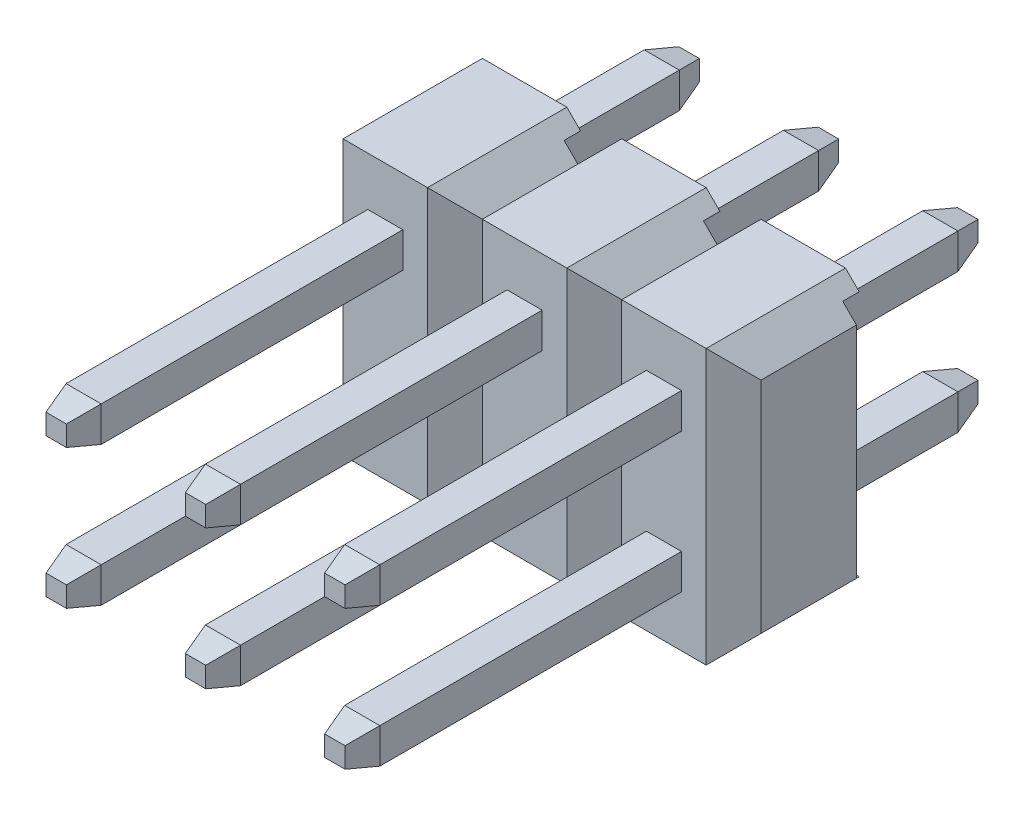
SolidWorks part; units mm, degrees
ref_plane "Front Plane" through (0, 0, 0) normal (0, 0, 1) x (1, 0, 0)
ref_plane "Top Plane" through (0, 0, 0) normal (0, 1, 0) x (1, 0, 0)
ref_plane "Right Plane" through (0, 0, 0) normal (1, 0, 0) x (0, 0, -1)
sketch "Sketch2" plane through (0, 0, 0) normal (0, 0, 1) x (1, 0, 0)
  line L1 (0, 0) -> (2.54, 0)
  line L2 (0, 0) -> (0, 5)
  line L3 (0, 5) -> (2.54, 5)
  line L4 (2.54, 0) -> (2.54, 5)
  dimension "length" = 2.54
  dimension "width" = 5
extrude "Boss-Extrude1" add sketch "Sketch2" along normal blind 2.54
sketch "Sketch3" plane through (0, 0, 0) normal (-1, 0, 0) x (0, 0, 1)
  line L0 (0, 2.5) -> (2.54, 2.5) construction
  line L1 (0, 5) -> (0, 0) construction
  line L2 (2.54, 5) -> (2.54, 0) construction
  line L3 (2.54, 5) -> (0, 5) construction
  line L4 (0, 4.75) -> (0.3, 4.75)
  line L5 (0, 4.75) -> (0, 0.25)
  line L6 (0, 0.25) -> (0.3, 0.25)
  line L7 (0.3, 4.75) -> (0.3, 0.25)
  point P10 (0, 2.5)
  dimension "D1" = 0.25
  dimension "D2" = 0.3
extrude "Cut-Extrude1" cut sketch "Sketch3" against normal through all
chamfer "Chamfer1" distance 0.5 angle 45 4 edges at (2.54, 5, 1.27) (2.54, 0, 1.27) (0, 5, 1.27) (0, 0, 1.27)
chamfer "Chamfer2" distance 0.5 angle 45 2 edges at (2.54, 2.5, 2.54) (0, 2.5, 2.54)
sketch "Sketch4" plane through (0, 0, 2.54) normal (0, 0, 1) x (1, 0, 0)
  line L0 (0.5, 1.25) -> (2.04, 1.25) construction
  line L1 (0.5, 5) -> (0.5, 0) construction
  line L2 (2.04, 0) -> (2.04, 5) construction
  line L3 (0.5, 0) -> (2.04, 0) construction
  line L4 (1.27, 5) -> (1.27, 0) construction
  line L5 (2.04, 5) -> (0.5, 5) construction
  line L7 (0.95, 1.57) -> (1.59, 1.57)
  line L8 (0.95, 1.57) -> (0.95, 0.93)
  line L9 (0.95, 0.93) -> (1.59, 0.93)
  line L10 (1.59, 1.57) -> (1.59, 0.93)
  point P16 (1.59, 1.25)
  point P17 (1.27, 1.57)
  dimension "D1" = 1.25
  dimension "D2" = 0.64
extrude "Boss-Extrude2" add sketch "Sketch4" along normal blind 6 separate body
sketch "Sketch6" plane through (0, 0, 0.3) normal (0, 0, -1) x (-1, 0, 0)
  line L1 (-1.59, 1.57) -> (-0.95, 1.57)
  line L2 (-1.59, 1.57) -> (-1.59, 0.93)
  line L3 (-1.59, 0.93) -> (-0.95, 0.93)
  line L4 (-0.95, 1.57) -> (-0.95, 0.93)
extrude "Boss-Extrude3" add sketch "Sketch6" along normal blind 3.3 separate body
chamfer "Chamfer3" distance 0.5 angle 15 4 edges at (1.27, 1.57, 8.54) (1.59, 1.25, 8.54) (1.27, 0.93, 8.54) (0.95, 1.25, 8.54)
chamfer "Chamfer4" distance 0.5 angle 15 4 edges at (1.27, 1.57, -3) (0.95, 1.25, -3) (1.27, 0.93, -3) (1.59, 1.25, -3)
pattern_linear "LPattern11" count 2 spacing 2.54 along (0, 1, 0) of bodies 104 103
pattern_linear "LPattern12" count 3 spacing 2.54 along (-1, 0, 0) of bodies 102
pattern_linear "LPattern13" count 3 spacing 2.54 along (-1, 0, 0) of bodies 104 110 103 111
equation "\"pins\" = 3"
equation "\"rows\"= 2"
equation "\"width@Sketch2\"= \"rows\" * 2.5"
equation "\"D1@LPattern11\"= \"rows\""
equation "\"D1@LPattern12\"= \"pins\""
equation "\"D1@LPattern11\"=\"rows\""
equation "\"D1@LPattern13\"=\"pins\""
